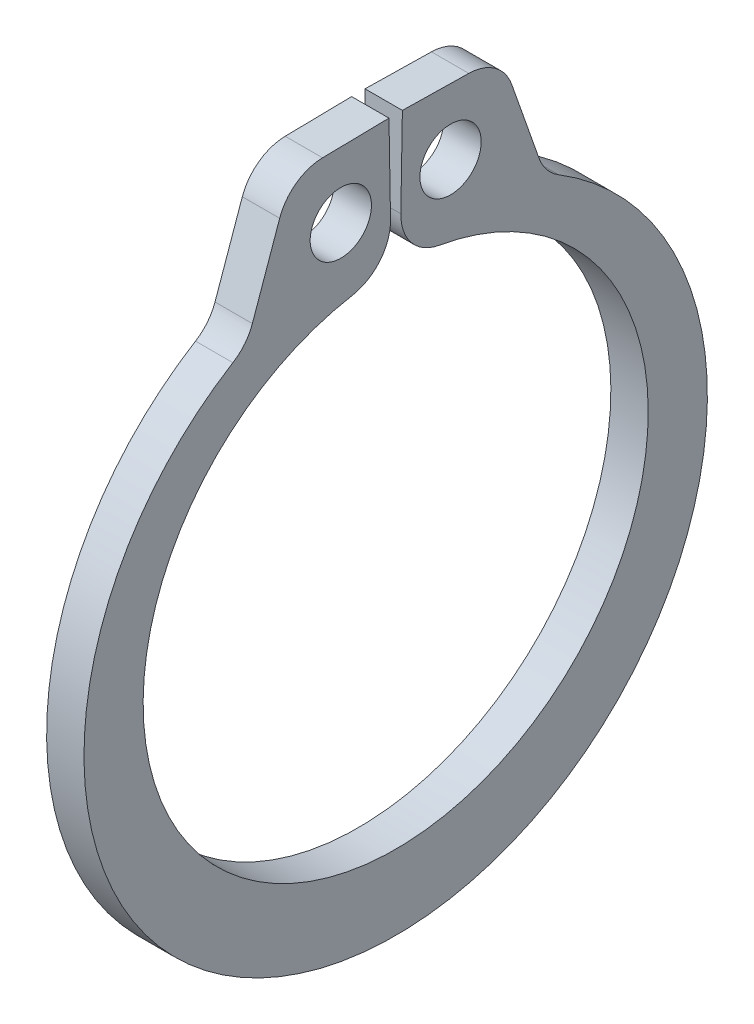
SolidWorks part; units mm, degrees
material "Cast Carbon Steel"
ref_plane "Front" through (0, 0, 0) normal (0, 0, 1) x (1, 0, 0)
ref_plane "Top" through (0, 0, 0) normal (0, 1, 0) x (1, 0, 0)
ref_plane "Right" through (0, 0, 0) normal (1, 0, 0) x (0, 0, -1)
sketch "Sketch1" plane through (0, 0, 0) normal (1, 0, 0) x (0, 0, -1)
  line L0 (0, 0) -> (0, 4.2926) construction
  line L1 (-0.0749, 4.2919) -> (-0.1139, 6.5268)
  line L2 (0.1139, 6.5268) -> (1.7901, 6.4975)
  line L3 (1.7901, 6.4975) -> (2.5323, 4.3892)
  line L4 (0.0749, 4.2919) -> (0.1139, 6.5268)
  line L5 (-0.1139, 6.5268) -> (-1.7901, 6.4975)
  line L6 (-1.7901, 6.4975) -> (-2.5323, 4.3892)
  line L7 (-2.5323, 4.3892) -> (-2.1452, 3.7182) construction
  line L8 (2.5323, 4.3892) -> (2.1452, 3.7182) construction
  line L9 (0, -4.2926) -> (0, -5.5626) construction
  line L10 (-1.7901, 6.4975) -> (-0.0749, 4.2919) construction
  line L11 (0, 4.2926) -> (0, 6.5278) construction
  line L12 (-4.2926, 0) -> (4.2926, 0) construction
  circle A0 centre (0, 0) radius 4.2926 construction
  arc A1 (-0.0749, 4.2919) -> (0.0749, 4.2919) centre (0, 0) ccw
  circle A4 centre (-0.9325, 5.3947) radius 0.5207
  circle A5 centre (0.9325, 5.3947) radius 0.5207
  arc A6 (-2.5323, 4.3892) -> (2.5323, 4.3892) centre (0, -0.2645) ccw construction
  point P0 (0, -5.5626)
  dimension "Ring ID" = 8.5852
  dimension "Hole Diameter" = 1.0414
  dimension "Min. Sec." = 0.7747
  dimension "Max. Sec." = 1.27
  dimension "Lug Height" = 2.2352
  dimension "D2" = 1.6764
  dimension "Angle" = 1
sketch "Sketch2" plane through (0, 0, 0) normal (0, 1, 0) x (1, 0, 0)
  line L0 (-0.3175, -5.2915) -> (0.3175, -5.2915) construction
  line L1 (0, -5.2981) -> (0, 5.2981) construction
  point P8 (0, -5.2915)
  dimension "Ring Thickness" = 0.635
sketch "Sketch3" plane through (0, 0, 0) normal (1, 0, 0) x (0, 0, -1)
  line L0 (-1.7901, 6.4975) -> (-2.5323, 4.3892) construction
  line L1 (-1.7901, 6.4975) -> (-2.5323, 4.3892)
  line L2 (-0.1139, 6.5268) -> (-1.7901, 6.4975) construction
  line L3 (-0.1139, 6.5268) -> (-1.7901, 6.4975)
  line L4 (-0.0749, 4.2919) -> (-0.1139, 6.5268) construction
  line L5 (-0.0749, 4.2919) -> (-0.1139, 6.5268)
  line L6 (0.0749, 4.2919) -> (0.1139, 6.5268) construction
  line L7 (0.0749, 4.2919) -> (0.1139, 6.5268)
  line L8 (0.1139, 6.5268) -> (1.7901, 6.4975) construction
  line L9 (0.1139, 6.5268) -> (1.7901, 6.4975)
  line L10 (1.7901, 6.4975) -> (2.5323, 4.3892) construction
  line L11 (1.7901, 6.4975) -> (2.5323, 4.3892)
  arc A0 (-2.5323, 4.3892) -> (2.5323, 4.3892) centre (0, -0.2645) ccw construction
  arc A1 (-2.5323, 4.3892) -> (2.5323, 4.3892) centre (0, -0.2645) ccw
  arc A2 (-0.0749, 4.2919) -> (0.0749, 4.2919) centre (0, 0) ccw construction
  arc A3 (-0.0749, 4.2919) -> (0.0749, 4.2919) centre (0, 0) ccw
  circle A4 centre (-0.9325, 5.3947) radius 0.5207 construction
  circle A5 centre (-0.9325, 5.3947) radius 0.5207
  circle A6 centre (0.9325, 5.3947) radius 0.5207 construction
  circle A7 centre (0.9325, 5.3947) radius 0.5207
extrude "Boss-Extrude1" add sketch "Sketch3" along normal up to vertex (0.3175 mm away) and the other way up to vertex (0.3175 mm away) up to point (0.3175, 0, 5.2915) other way up to point (-0.3175, 0, 5.2915)
fillet "Fillet1" radius 0.7874 6 edges at (0, 4.3892, -2.5323) (0, 6.4975, -1.7901) (0, 4.2919, -0.0749) (0, 4.2919, 0.0749) (0, 6.4975, 1.7901) (0, 4.3892, 2.5323)
sketch "Sketch4" plane through (0, 0, 0) normal (1, 0, 0) x (0, 0, -1)
  line L0 (-3.7175, 2.1463) -> (0, 0) construction
  line L1 (0, 0) -> (0, 4.2926) construction
  line L2 (0, 6.5278) -> (0, 4.2926) construction
  arc A0 (-0.0749, 4.2919) -> (0.0749, 4.2919) centre (0, 0) ccw construction
  point P0 (0, 0)
  point P1 (-3.7175, 2.1463)
  dimension "D1" = 60
equation "\"D2@Sketch1\" = \"Lug Height@Sketch1\" * .75"
